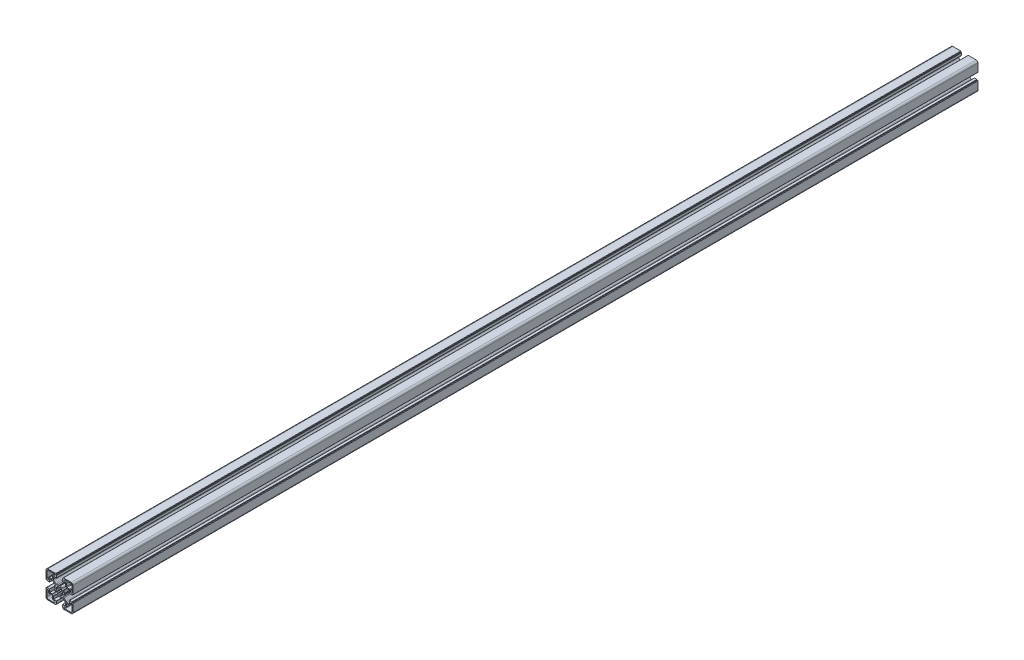
SolidWorks part; units mm, degrees
ref_plane "Front Plane" through (0, 0, 0) normal (0, 0, 1) x (1, 0, 0)
ref_plane "Top Plane" through (0, 0, 0) normal (0, 1, 0) x (1, 0, 0)
ref_plane "Right Plane" through (0, 0, 0) normal (1, 0, 0) x (0, 0, -1)
sketch "Sketch1" plane through (0, 0, 0) normal (0, 0, 1) x (1, 0, 0)
  line L0 (10.55, 18) -> (9, 18)
  line L1 (18.5, 21) -> (9, 21)
  line L2 (21, 9.0002) -> (21, 18.5)
  line L3 (18, 9.0002) -> (18, 10.55)
  line L4 (17, 11.55) -> (12.55, 11.55)
  line L5 (11.55, 12.55) -> (11.55, 17)
  line L6 (7.974, 0.7926) -> (7.5401, 0.0468)
  line L7 (-0.8674, 4.9242) -> (-0.9675, 5.4811)
  line L8 (-3.1913, 4.5626) -> (-2.864, 4.0985)
  line L9 (-4.0897, 2.8765) -> (-4.5668, 3.2082)
  line L10 (-5.4897, 0.9862) -> (-4.9205, 0.8878)
  line L11 (11.1298, 9.425) -> (7.5635, 5.8587)
  line L12 (16.3169, 9.9945) -> (12.5048, 9.9945)
  line L13 (16.5169, 5.2) -> (16.5169, 9.7945)
  line L14 (20.7196, 5) -> (16.7169, 5)
  line L15 (21.0196, 5.3) -> (21.0196, 5.5)
  line L16 (22, 5.8) -> (21.3196, 5.8)
  line L17 (22.5, 6.3) -> (22.5, 19.5)
  line L18 (19.5, 22.5) -> (6.3757, 22.5)
  line L19 (5.8757, 21.3) -> (5.8757, 22)
  line L20 (5.5757, 21) -> (5.3, 21)
  line L21 (5, 16.6668) -> (5, 20.7)
  line L22 (9.9054, 16.4668) -> (5.2, 16.4668)
  line L23 (10.1054, 12.4716) -> (10.1054, 16.2668)
  line L24 (5.9449, 7.4827) -> (9.5196, 11.0574)
  line L25 (0.1126, 7.6069) -> (0.7547, 7.9748)
  line L26 (5.4897, 0.9862) -> (4.9205, 0.8878)
  line L27 (4.0897, 2.8765) -> (4.5668, 3.2082)
  line L28 (3.1913, 4.5626) -> (2.864, 4.0985)
  line L29 (0.8674, 4.9242) -> (0.9675, 5.4811)
  line L30 (-10.55, -18) -> (-9, -18)
  line L31 (-18.5, -21) -> (-9, -21)
  line L32 (-21, -9.0002) -> (-21, -18.5)
  line L33 (-18, -9.0002) -> (-18, -10.55)
  line L34 (-17, -11.55) -> (-12.55, -11.55)
  line L35 (-11.55, -12.55) -> (-11.55, -17)
  line L36 (-7.974, -0.7926) -> (-7.5401, -0.0468)
  line L37 (-11.1298, -9.425) -> (-7.5635, -5.8587)
  line L38 (-16.3169, -9.9945) -> (-12.5048, -9.9945)
  line L39 (-16.5169, -5.2) -> (-16.5169, -9.7945)
  line L40 (-20.7196, -5) -> (-16.7169, -5)
  line L41 (-21.0196, -5.3) -> (-21.0196, -5.5)
  line L42 (-22, -5.8) -> (-21.3196, -5.8)
  line L43 (-22.5, -6.3) -> (-22.5, -19.5)
  line L44 (-19.5, -22.5) -> (-6.3757, -22.5)
  line L45 (-5.8757, -21.3) -> (-5.8757, -22)
  line L46 (-5.5757, -21) -> (-5.3, -21)
  line L47 (-5, -16.6668) -> (-5, -20.7)
  line L48 (-9.9054, -16.4668) -> (-5.2, -16.4668)
  line L49 (-10.1054, -12.4716) -> (-10.1054, -16.2668)
  line L50 (-5.9449, -7.4827) -> (-9.5196, -11.0574)
  line L51 (-0.1126, -7.6069) -> (-0.7547, -7.9748)
  line L52 (0.8674, -4.9242) -> (0.9675, -5.4811)
  line L53 (3.1913, -4.5626) -> (2.864, -4.0985)
  line L54 (4.0897, -2.8765) -> (4.5668, -3.2082)
  line L55 (5.4897, -0.9862) -> (4.9205, -0.8878)
  line L56 (0.1126, -7.6069) -> (0.7547, -7.9748)
  line L57 (5.9449, -7.4827) -> (9.5196, -11.0574)
  line L58 (10.1054, -12.4716) -> (10.1054, -16.2668)
  line L59 (9.9054, -16.4668) -> (5.2, -16.4668)
  line L60 (5, -16.6668) -> (5, -20.7)
  line L61 (5.5757, -21) -> (5.3, -21)
  line L62 (-0.1126, 7.6069) -> (-0.7547, 7.9748)
  line L63 (-5.9449, 7.4827) -> (-9.5196, 11.0574)
  line L64 (-10.1054, 12.4716) -> (-10.1054, 16.2668)
  line L65 (-9.9054, 16.4668) -> (-5.2, 16.4668)
  line L66 (-5, 16.6668) -> (-5, 20.7)
  line L67 (-5.5757, 21) -> (-5.3, 21)
  line L68 (-5.8757, 21.3) -> (-5.8757, 22)
  line L69 (-19.5, 22.5) -> (-6.3757, 22.5)
  line L70 (-22.5, 6.3) -> (-22.5, 19.5)
  line L71 (-22, 5.8) -> (-21.3196, 5.8)
  line L72 (-21.0196, 5.3) -> (-21.0196, 5.5)
  line L73 (-20.7196, 5) -> (-16.7169, 5)
  line L74 (-16.5169, 5.2) -> (-16.5169, 9.7945)
  line L75 (-16.3169, 9.9945) -> (-12.5048, 9.9945)
  line L76 (-11.1298, 9.425) -> (-7.5635, 5.8587)
  line L77 (-7.974, 0.7926) -> (-7.5401, 0.0468)
  line L78 (5.8757, -21.3) -> (5.8757, -22)
  line L79 (19.5, -22.5) -> (6.3757, -22.5)
  line L80 (22.5, -6.3) -> (22.5, -19.5)
  line L81 (22, -5.8) -> (21.3196, -5.8)
  line L82 (21.0196, -5.3) -> (21.0196, -5.5)
  line L83 (20.7196, -5) -> (16.7169, -5)
  line L84 (16.5169, -5.2) -> (16.5169, -9.7945)
  line L85 (16.3169, -9.9945) -> (12.5048, -9.9945)
  line L86 (11.1298, -9.425) -> (7.5635, -5.8587)
  line L87 (-5.4897, -0.9862) -> (-4.9205, -0.8878)
  line L88 (-4.0897, -2.8765) -> (-4.5668, -3.2082)
  line L89 (-3.1913, -4.5626) -> (-2.864, -4.0985)
  line L90 (-0.8674, -4.9242) -> (-0.9675, -5.4811)
  line L91 (7.974, -0.7926) -> (7.5401, -0.0468)
  line L92 (-11.55, 12.55) -> (-11.55, 17)
  line L93 (-17, 11.55) -> (-12.55, 11.55)
  line L94 (-18, 9.0002) -> (-18, 10.55)
  line L95 (-21, 9.0002) -> (-21, 18.5)
  line L96 (-18.5, 21) -> (-9, 21)
  line L97 (-10.55, 18) -> (-9, 18)
  line L98 (11.55, -12.55) -> (11.55, -17)
  line L99 (17, -11.55) -> (12.55, -11.55)
  line L100 (18, -9.0002) -> (18, -10.55)
  line L101 (21, -9.0002) -> (21, -18.5)
  line L102 (18.5, -21) -> (9, -21)
  line L103 (10.55, -18) -> (9, -18)
  line L104 (-33.3633, 0) -> (37.7265, 0) construction
  line L105 (0, 32.2957) -> (0, -36.0465) construction
  arc A0 (9, 18) -> (9, 21) centre (9, 19.5) cw
  arc A1 (18.5, 21) -> (21, 18.5) centre (18.5, 18.5) cw
  arc A2 (21, 9.0002) -> (18, 9.0002) centre (19.5, 9.0002) cw
  arc A3 (17, 11.55) -> (18, 10.55) centre (17, 10.55) cw
  arc A4 (12.55, 11.55) -> (11.55, 12.55) centre (12.55, 12.55) cw
  arc A5 (10.55, 18) -> (11.55, 17) centre (10.55, 17) cw
  arc A6 (7.5313, 0) -> (7.5401, 0.0468) centre (7.7309, -0.013) cw
  arc A7 (8, 0.9141) -> (7.974, 0.7926) centre (7.8011, 0.8932) cw
  arc A8 (7.2004, 3.6119) -> (8, 0.9141) centre (0.0496, 0.0249) cw
  arc A9 (7.2004, 3.6119) -> (7.5635, 5.8587) centre (8.9385, 4.4837) cw
  arc A10 (11.1298, 9.425) -> (12.5048, 9.9945) centre (12.5048, 8.05) cw
  arc A11 (16.3169, 9.9945) -> (16.5169, 9.7945) centre (16.3169, 9.7945) cw
  arc A12 (16.7169, 5) -> (16.5169, 5.2) centre (16.7169, 5.2) cw
  arc A13 (21.0196, 5.3) -> (20.7196, 5) centre (20.7196, 5.3) cw
  arc A14 (0.8674, 4.9242) -> (-0.8674, 4.9242) centre (0, 0) ccw
  arc A15 (-0.9675, 5.4811) -> (-1.5951, 5.8941) centre (-1.4627, 5.4119) ccw
  arc A16 (-1.5951, 5.8941) -> (-3.0444, 5.2994) centre (-0.0235, 0) ccw
  arc A17 (-3.0444, 5.2994) -> (-3.1913, 4.5626) centre (-2.7943, 4.8665) ccw
  arc A18 (-2.864, 4.0985) -> (-4.0897, 2.8765) centre (0, 0) ccw
  arc A19 (-4.5668, 3.2082) -> (-5.3025, 3.0565) centre (-4.868, 2.8091) ccw
  arc A20 (-5.3025, 3.0565) -> (-5.9068, 1.6112) centre (-0.0235, 0) ccw
  arc A21 (-5.9068, 1.6112) -> (-5.4897, 0.9862) centre (-5.4239, 1.4819) ccw
  arc A22 (-4.9205, 0.8878) -> (-5, 0) centre (0, 0) ccw
  arc A23 (21.0196, 5.5) -> (21.3196, 5.8) centre (21.3196, 5.5) cw
  arc A24 (22.5, 6.3) -> (22, 5.8) centre (22, 6.3) cw
  arc A25 (19.5, 22.5) -> (22.5, 19.5) centre (19.5, 19.5) cw
  arc A26 (5.8757, 22) -> (6.3757, 22.5) centre (6.3757, 22) cw
  arc A27 (5.8757, 21.3) -> (5.5757, 21) centre (5.5757, 21.3) cw
  arc A28 (5, 20.7) -> (5.3, 21) centre (5.3, 20.7) cw
  arc A29 (5.2, 16.4668) -> (5, 16.6668) centre (5.2, 16.6668) cw
  arc A30 (9.9054, 16.4668) -> (10.1054, 16.2668) centre (9.9054, 16.2668) cw
  arc A31 (10.1054, 12.4716) -> (9.5196, 11.0574) centre (8.1054, 12.4716) cw
  arc A32 (5.9449, 7.4827) -> (3.6665, 7.1733) centre (4.5855, 8.9496) cw
  arc A33 (0.8764, 8) -> (3.6665, 7.1733) centre (0.0235, 0) cw
  arc A34 (0.7547, 7.9748) -> (0.8764, 8) centre (0.8542, 7.8013) cw
  arc A35 (0.1126, 7.6069) -> (0, 7.531) centre (-0.0489, 7.7249) cw
  arc A36 (4.9205, 0.8878) -> (5, 0) centre (0, 0) cw
  arc A37 (5.9068, 1.6112) -> (5.4897, 0.9862) centre (5.4239, 1.4819) cw
  arc A38 (5.3025, 3.0565) -> (5.9068, 1.6112) centre (0.0235, 0) cw
  arc A39 (4.5668, 3.2082) -> (5.3025, 3.0565) centre (4.868, 2.8091) cw
  arc A40 (2.864, 4.0985) -> (4.0897, 2.8765) centre (0, 0) cw
  arc A41 (3.0444, 5.2994) -> (3.1913, 4.5626) centre (2.7943, 4.8665) cw
  arc A42 (1.5951, 5.8941) -> (3.0444, 5.2994) centre (0.0235, 0) cw
  arc A43 (0.9675, 5.4811) -> (1.5951, 5.8941) centre (1.4627, 5.4119) cw
  arc A44 (-9, -18) -> (-9, -21) centre (-9, -19.5) cw
  arc A45 (-18.5, -21) -> (-21, -18.5) centre (-18.5, -18.5) cw
  arc A46 (-21, -9.0002) -> (-18, -9.0002) centre (-19.5, -9.0002) cw
  arc A47 (-17, -11.55) -> (-18, -10.55) centre (-17, -10.55) cw
  arc A48 (-12.55, -11.55) -> (-11.55, -12.55) centre (-12.55, -12.55) cw
  arc A49 (-10.55, -18) -> (-11.55, -17) centre (-10.55, -17) cw
  arc A50 (-7.5313, 0) -> (-7.5401, -0.0468) centre (-7.7309, 0.013) cw
  arc A51 (-8, -0.9141) -> (-7.974, -0.7926) centre (-7.8011, -0.8932) cw
  arc A52 (-7.2004, -3.6119) -> (-8, -0.9141) centre (-0.0496, -0.0249) cw
  arc A53 (-7.2004, -3.6119) -> (-7.5635, -5.8587) centre (-8.9385, -4.4837) cw
  arc A54 (-11.1298, -9.425) -> (-12.5048, -9.9945) centre (-12.5048, -8.05) cw
  arc A55 (-16.3169, -9.9945) -> (-16.5169, -9.7945) centre (-16.3169, -9.7945) cw
  arc A56 (-16.7169, -5) -> (-16.5169, -5.2) centre (-16.7169, -5.2) cw
  arc A57 (-21.0196, -5.3) -> (-20.7196, -5) centre (-20.7196, -5.3) cw
  arc A58 (-21.0196, -5.5) -> (-21.3196, -5.8) centre (-21.3196, -5.5) cw
  arc A59 (-22.5, -6.3) -> (-22, -5.8) centre (-22, -6.3) cw
  arc A60 (-19.5, -22.5) -> (-22.5, -19.5) centre (-19.5, -19.5) cw
  arc A61 (-5.8757, -22) -> (-6.3757, -22.5) centre (-6.3757, -22) cw
  arc A62 (-5.8757, -21.3) -> (-5.5757, -21) centre (-5.5757, -21.3) cw
  arc A63 (-5, -20.7) -> (-5.3, -21) centre (-5.3, -20.7) cw
  arc A64 (-5.2, -16.4668) -> (-5, -16.6668) centre (-5.2, -16.6668) cw
  arc A65 (-9.9054, -16.4668) -> (-10.1054, -16.2668) centre (-9.9054, -16.2668) cw
  arc A66 (-10.1054, -12.4716) -> (-9.5196, -11.0574) centre (-8.1054, -12.4716) cw
  arc A67 (-5.9449, -7.4827) -> (-3.6665, -7.1733) centre (-4.5855, -8.9496) cw
  arc A68 (-0.8764, -8) -> (-3.6665, -7.1733) centre (-0.0235, 0) cw
  arc A69 (-0.7547, -7.9748) -> (-0.8764, -8) centre (-0.8542, -7.8013) cw
  arc A70 (-0.1126, -7.6069) -> (0, -7.531) centre (0.0489, -7.7249) cw
  arc A71 (0.9675, -5.4811) -> (1.5951, -5.8941) centre (1.4627, -5.4119) ccw
  arc A72 (1.5951, -5.8941) -> (3.0444, -5.2994) centre (0.0235, 0) ccw
  arc A73 (3.0444, -5.2994) -> (3.1913, -4.5626) centre (2.7943, -4.8665) ccw
  arc A74 (2.864, -4.0985) -> (4.0897, -2.8765) centre (0, 0) ccw
  arc A75 (4.5668, -3.2082) -> (5.3025, -3.0565) centre (4.868, -2.8091) ccw
  arc A76 (5.3025, -3.0565) -> (5.9068, -1.6112) centre (0.0235, 0) ccw
  arc A77 (5.9068, -1.6112) -> (5.4897, -0.9862) centre (5.4239, -1.4819) ccw
  arc A78 (4.9205, -0.8878) -> (5, 0) centre (0, 0) ccw
  arc A79 (0.1126, -7.6069) -> (0, -7.531) centre (-0.0489, -7.7249) ccw
  arc A80 (0.7547, -7.9748) -> (0.8764, -8) centre (0.8542, -7.8013) ccw
  arc A81 (0.8764, -8) -> (3.6665, -7.1733) centre (0.0235, 0) ccw
  arc A82 (5.9449, -7.4827) -> (3.6665, -7.1733) centre (4.5855, -8.9496) ccw
  arc A83 (10.1054, -12.4716) -> (9.5196, -11.0574) centre (8.1054, -12.4716) ccw
  arc A84 (9.9054, -16.4668) -> (10.1054, -16.2668) centre (9.9054, -16.2668) ccw
  arc A85 (5.2, -16.4668) -> (5, -16.6668) centre (5.2, -16.6668) ccw
  arc A86 (5, -20.7) -> (5.3, -21) centre (5.3, -20.7) ccw
  arc A87 (5.8757, -21.3) -> (5.5757, -21) centre (5.5757, -21.3) ccw
  arc A88 (-0.1126, 7.6069) -> (0, 7.531) centre (0.0489, 7.7249) ccw
  arc A89 (-0.7547, 7.9748) -> (-0.8764, 8) centre (-0.8542, 7.8013) ccw
  arc A90 (-0.8764, 8) -> (-3.6665, 7.1733) centre (-0.0235, 0) ccw
  arc A91 (-5.9449, 7.4827) -> (-3.6665, 7.1733) centre (-4.5855, 8.9496) ccw
  arc A92 (-10.1054, 12.4716) -> (-9.5196, 11.0574) centre (-8.1054, 12.4716) ccw
  arc A93 (-9.9054, 16.4668) -> (-10.1054, 16.2668) centre (-9.9054, 16.2668) ccw
  arc A94 (-5.2, 16.4668) -> (-5, 16.6668) centre (-5.2, 16.6668) ccw
  arc A95 (-5, 20.7) -> (-5.3, 21) centre (-5.3, 20.7) ccw
  arc A96 (-5.8757, 21.3) -> (-5.5757, 21) centre (-5.5757, 21.3) ccw
  arc A97 (-5.8757, 22) -> (-6.3757, 22.5) centre (-6.3757, 22) ccw
  arc A98 (-19.5, 22.5) -> (-22.5, 19.5) centre (-19.5, 19.5) ccw
  arc A99 (-22.5, 6.3) -> (-22, 5.8) centre (-22, 6.3) ccw
  arc A100 (-21.0196, 5.5) -> (-21.3196, 5.8) centre (-21.3196, 5.5) ccw
  arc A101 (-21.0196, 5.3) -> (-20.7196, 5) centre (-20.7196, 5.3) ccw
  arc A102 (-16.7169, 5) -> (-16.5169, 5.2) centre (-16.7169, 5.2) ccw
  arc A103 (-16.3169, 9.9945) -> (-16.5169, 9.7945) centre (-16.3169, 9.7945) ccw
  arc A104 (-11.1298, 9.425) -> (-12.5048, 9.9945) centre (-12.5048, 8.05) ccw
  arc A105 (-7.2004, 3.6119) -> (-7.5635, 5.8587) centre (-8.9385, 4.4837) ccw
  arc A106 (-7.2004, 3.6119) -> (-8, 0.9141) centre (-0.0496, 0.0249) ccw
  arc A107 (-8, 0.9141) -> (-7.974, 0.7926) centre (-7.8011, 0.8932) ccw
  arc A108 (-7.5313, 0) -> (-7.5401, 0.0468) centre (-7.7309, -0.013) ccw
  arc A109 (5.8757, -22) -> (6.3757, -22.5) centre (6.3757, -22) ccw
  arc A110 (19.5, -22.5) -> (22.5, -19.5) centre (19.5, -19.5) ccw
  arc A111 (22.5, -6.3) -> (22, -5.8) centre (22, -6.3) ccw
  arc A112 (21.0196, -5.5) -> (21.3196, -5.8) centre (21.3196, -5.5) ccw
  arc A113 (-4.9205, -0.8878) -> (-5, 0) centre (0, 0) cw
  arc A114 (-5.9068, -1.6112) -> (-5.4897, -0.9862) centre (-5.4239, -1.4819) cw
  arc A115 (-5.3025, -3.0565) -> (-5.9068, -1.6112) centre (-0.0235, 0) cw
  arc A116 (-4.5668, -3.2082) -> (-5.3025, -3.0565) centre (-4.868, -2.8091) cw
  arc A117 (-2.864, -4.0985) -> (-4.0897, -2.8765) centre (0, 0) cw
  arc A118 (-3.0444, -5.2994) -> (-3.1913, -4.5626) centre (-2.7943, -4.8665) cw
  arc A119 (-1.5951, -5.8941) -> (-3.0444, -5.2994) centre (-0.0235, 0) cw
  arc A120 (-0.9675, -5.4811) -> (-1.5951, -5.8941) centre (-1.4627, -5.4119) cw
  arc A121 (0.8674, -4.9242) -> (-0.8674, -4.9242) centre (0, 0) cw
  arc A122 (21.0196, -5.3) -> (20.7196, -5) centre (20.7196, -5.3) ccw
  arc A123 (16.7169, -5) -> (16.5169, -5.2) centre (16.7169, -5.2) ccw
  arc A124 (-10.55, 18) -> (-11.55, 17) centre (-10.55, 17) ccw
  arc A125 (-12.55, 11.55) -> (-11.55, 12.55) centre (-12.55, 12.55) ccw
  arc A126 (-17, 11.55) -> (-18, 10.55) centre (-17, 10.55) ccw
  arc A127 (-21, 9.0002) -> (-18, 9.0002) centre (-19.5, 9.0002) ccw
  arc A128 (-18.5, 21) -> (-21, 18.5) centre (-18.5, 18.5) ccw
  arc A129 (-9, 18) -> (-9, 21) centre (-9, 19.5) ccw
  arc A130 (16.3169, -9.9945) -> (16.5169, -9.7945) centre (16.3169, -9.7945) ccw
  arc A131 (11.1298, -9.425) -> (12.5048, -9.9945) centre (12.5048, -8.05) ccw
  arc A132 (7.2004, -3.6119) -> (7.5635, -5.8587) centre (8.9385, -4.4837) ccw
  arc A133 (7.2004, -3.6119) -> (8, -0.9141) centre (0.0496, -0.0249) ccw
  arc A134 (8, -0.9141) -> (7.974, -0.7926) centre (7.8011, -0.8932) ccw
  arc A135 (7.5313, 0) -> (7.5401, -0.0468) centre (7.7309, 0.013) ccw
  arc A136 (10.55, -18) -> (11.55, -17) centre (10.55, -17) ccw
  arc A137 (12.55, -11.55) -> (11.55, -12.55) centre (12.55, -12.55) ccw
  arc A138 (17, -11.55) -> (18, -10.55) centre (17, -10.55) ccw
  arc A139 (21, -9.0002) -> (18, -9.0002) centre (19.5, -9.0002) ccw
  arc A140 (18.5, -21) -> (21, -18.5) centre (18.5, -18.5) ccw
  arc A141 (9, -18) -> (9, -21) centre (9, -19.5) ccw
  dimension "D6" = 12.2
  dimension "D8" = 10
  dimension "D1" = 10
  dimension "D2" = 45
  dimension "D3" = 45
  dimension "D4" = 10
  dimension "D5" = 14.5
  dimension "D7" = 22.5
extrude "Base-Extrude" add sketch "Sketch1" against normal blind 1510
